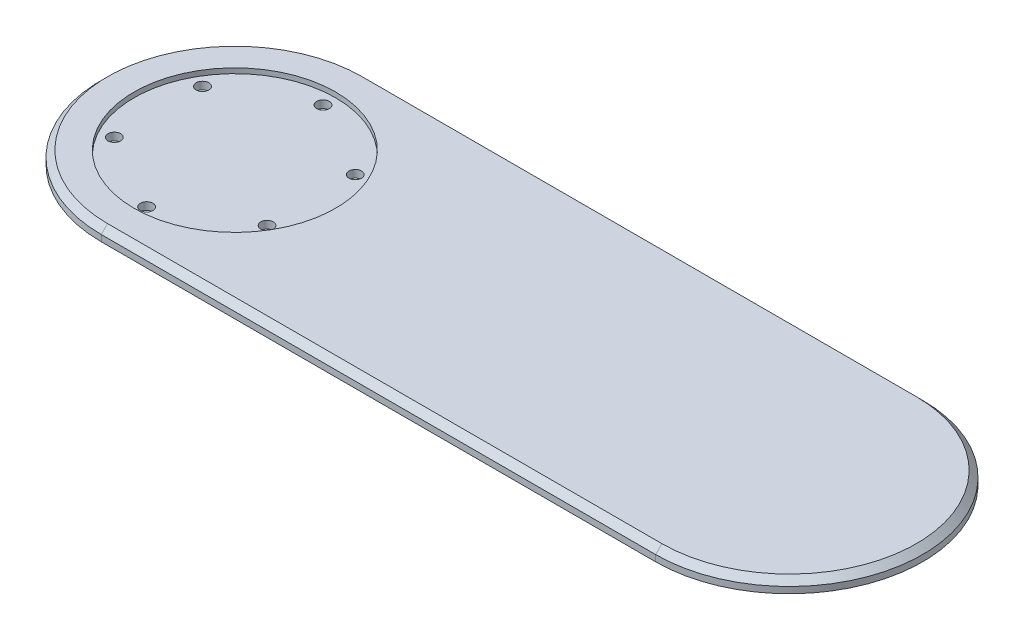
SolidWorks part; units mm, degrees
ref_plane "Front Plane" through (0, 0, 0) normal (0, 0, 1) x (1, 0, 0)
ref_plane "Top Plane" through (0, 0, 0) normal (0, 1, 0) x (1, 0, 0)
ref_plane "Right Plane" through (0, 0, 0) normal (1, 0, 0) x (0, 0, -1)
sketch "Sketch1" plane through (0, 0, 0) normal (0, 1, 0) x (1, 0, 0)
  line L0 (-110, 0) -> (-79.7951, 0) construction
  line L1 (-110, -53) -> (110, -53)
  line L2 (-110, -53) -> (-110, 53)
  line L3 (-110, 53) -> (110, 53)
  line L4 (110, -53) -> (110, 53)
  line L5 (-110, -53) -> (110, 53) construction
  line L6 (-110, 53) -> (110, -53) construction
  circle A0 centre (-110, 0) radius 53
  circle A1 centre (110, 0) radius 53
  circle A2 centre (-110, 0) radius 35 construction
  circle A3 centre (-110, 35) radius 2.5
  circle A4 centre (-79.6891, 17.5) radius 2.5
  circle A5 centre (-79.6891, -17.5) radius 2.5
  circle A6 centre (-110, -35) radius 2.5
  circle A7 centre (-140.3109, -17.5) radius 2.5
  circle A8 centre (-140.3109, 17.5) radius 2.5
  point P0 (0, 0)
  point P27 (-110, 0)
  dimension "D3" = 70
  dimension "D4" = 5
  dimension "D1" = 220
  dimension "D2" = 106
  dimension "D5" = 6
extrude "Boss-Extrude1" add sketch "Sketch1" along normal blind 5 contours L2 A0 | L2 A0 | A1 L3 A0 L1 | L4 A1 | L4 A1
sketch "Sketch2" plane through (0, 5, 0) normal (0, 1, 0) x (1, 0, 0)
  line L0 (-140.3109, 17.5) -> (-79.6891, -17.5) construction
  line L1 (-140.3109, -17.5) -> (-79.6891, 17.5) construction
  circle A0 centre (-110, 0) radius 40
  dimension "D1" = 80
extrude "Cut-Extrude1" cut sketch "Sketch2" against normal blind 2
chamfer "Chamfer1" distance 2.5 angle 45 4 edges at (163, 5, 0) (0, 5, -53) (-163, 5, 0) (0, 5, 53)
